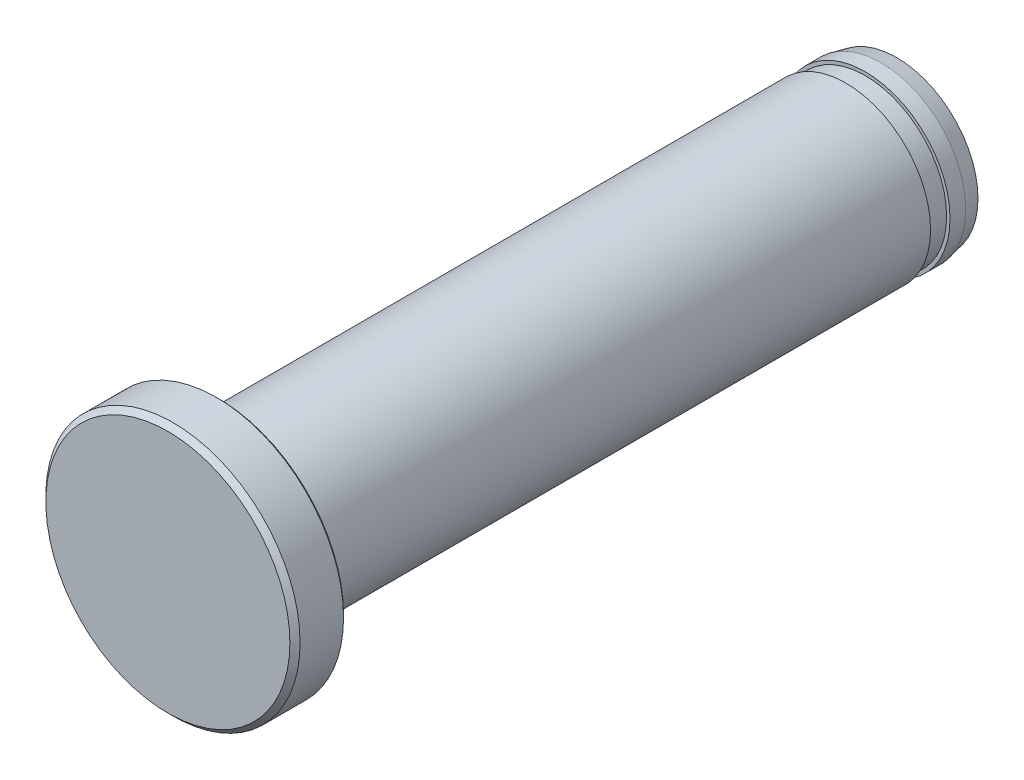
SolidWorks part; units mm, degrees
ref_plane "前视基准面" through (0, 0, 0) normal (0, 0, 1) x (1, 0, 0)
ref_plane "上视基准面" through (0, 0, 0) normal (0, 1, 0) x (1, 0, 0)
ref_plane "右视基准面" through (0, 0, 0) normal (1, 0, 0) x (0, 0, -1)
sketch "草图1" plane through (0, 0, 0) normal (1, 0, 0) x (0, 0, -1)
  line L0 (-18.5, 0) -> (18.5, 0) construction
  line L1 (18.5, 0) -> (21.5, 0)
  line L2 (21.5, 0) -> (21.5, 4.8)
  line L3 (21.5, 4.8) -> (20.575, 5)
  line L4 (20.575, 5) -> (19.65, 5)
  line L5 (19.65, 5) -> (19.65, 4.8)
  line L6 (19.65, 4.8) -> (18.5, 4.8)
  line L7 (18.5, 4.8) -> (18.5, 5)
  line L8 (18.5, 5) -> (0, 5)
  line L9 (0, 5) -> (0, 0)
  line L10 (20.575, 5) -> (21.5, 5) construction
  line L11 (-18.5, 0) -> (-18.5, 7.5)
  line L12 (-18.5, 7.5) -> (-21.2, 7.5)
  line L13 (-21.2, 7.5) -> (-21.5, 7.2)
  line L14 (-21.5, 7.2) -> (-21.5, 0)
  line L15 (-21.5, 0) -> (-18.5, 0)
  dimension "D1" = 45
  dimension "L" = 37
  dimension "Dg6" = 10
  dimension "d" = 9.6
  dimension "m" = 1.15
  dimension "(M)" = 3
  dimension "H" = 15
  dimension "T" = 3
  dimension "D2" = 0.3
sketch "草图3" plane through (0, 0, 0) normal (1, 0, 0) x (0, 0, -1)
  line L0 (18.5, 0) -> (21.5, 0) construction
  line L1 (21.5, 0) -> (21.5, 4.8) construction
  line L2 (21.5, 4.8) -> (20.575, 5) construction
  line L3 (20.575, 5) -> (19.65, 5) construction
  line L4 (19.65, 5) -> (19.65, 4.8) construction
  line L5 (19.65, 4.8) -> (18.5, 4.8) construction
  line L6 (18.5, 4.8) -> (18.5, 5) construction
  line L7 (18.5, 5) -> (0, 5) construction
  line L9 (18.5, 0) -> (21.5, 0)
  line L10 (21.5, 0) -> (21.5, 4.8)
  line L11 (21.5, 4.8) -> (20.575, 5)
  line L12 (20.575, 5) -> (19.65, 5)
  line L13 (19.65, 5) -> (19.65, 4.8)
  line L14 (19.65, 4.8) -> (18.5, 4.8)
  line L15 (18.5, 4.8) -> (18.5, 5)
  line L16 (18.5, 5) -> (0, 5)
  line L17 (0, 5) -> (-18.3333, 5)
  line L18 (-18.5, 0) -> (-18.5, 7.5) construction
  line L19 (-18.5, 5.1667) -> (-18.5, 7.3667)
  line L20 (-18.6333, 7.5) -> (-21.2, 7.5)
  line L21 (-21.2, 7.5) -> (-21.5, 7.2)
  line L22 (-21.5, 7.2) -> (-21.5, 0)
  line L23 (-21.5, 0) -> (18.5, 0)
  line L24 (-18.6333, 7.5) -> (-18.5, 7.3667)
  arc A0 (-18.5, 5.1667) -> (-18.3333, 5) centre (-18.3333, 5.1667) ccw
  point P22 (-18.5, 5)
  dimension "D1" = 0.1667
  dimension "D2" = 45
  dimension "D3" = 0.1333
revolve "旋转1" add sketch "草图3" angle 360 mid plane about L23
